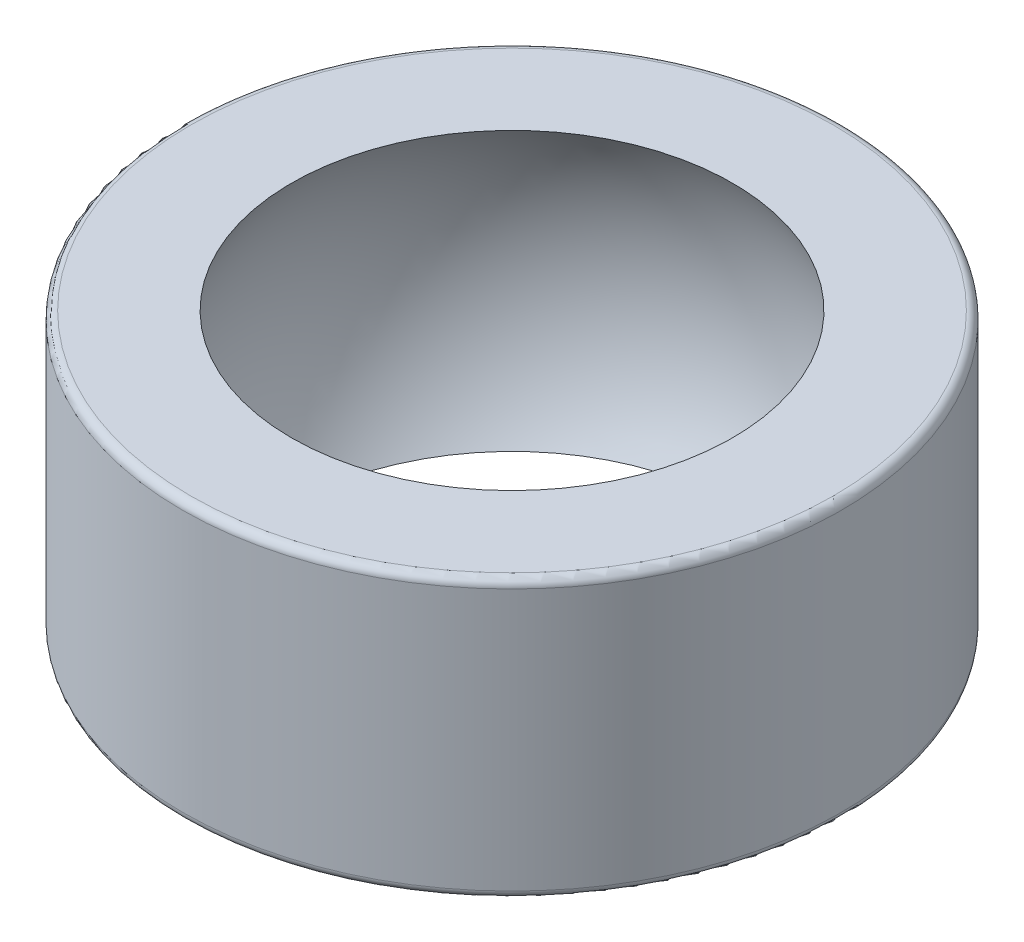
SolidWorks part; units mm, degrees
material "1.0545 (S355N)"
ref_plane "Płaszczyzna przednia" through (0, 0, 0) normal (0, 0, 1) x (1, 0, 0)
ref_plane "Płaszczyzna górna" through (0, 0, 0) normal (0, 1, 0) x (1, 0, 0)
ref_plane "Płaszczyzna prawa" through (0, 0, 0) normal (1, 0, 0) x (0, 0, -1)
sketch "Szkic1" plane through (0, 0, 0) normal (0, 1, 0) x (1, 0, 0)
  circle A0 centre (0, 0) radius 8
  dimension "d2" = 16
extrude "Dodanie-wyciągnięcie1" add sketch "Szkic1" along normal mid plane 6.75
sketch "Szkic3" plane through (0, 0, 0) normal (0, 0, 1) x (1, 0, 0)
  line L0 (0, -6.33) -> (0, 6.33)
  arc A0 (0, -6.33) -> (0, 6.33) centre (0, 0) ccw
  dimension "d3" = 12.66
revolve "Wycięcie-obrót1" cut sketch "Szkic3" angle 360 about L0
fillet "Zaokrąglenie1" radius 0.2 2 edges at (0, 3.375, 8) (0, -3.375, 8)
